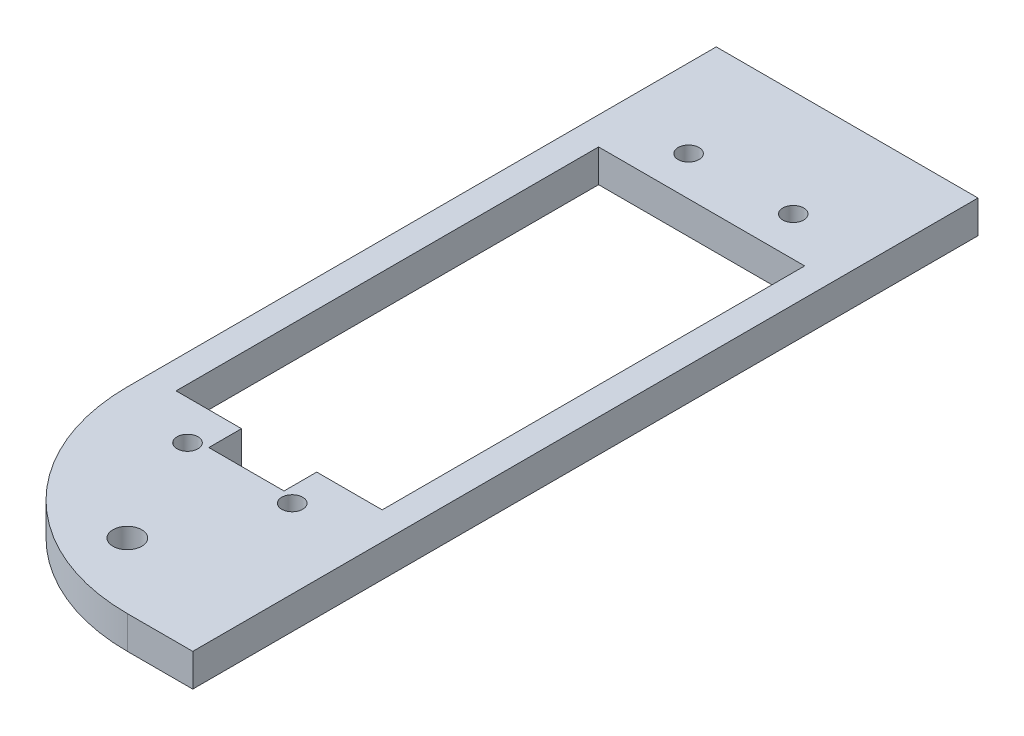
SolidWorks part; units mm, degrees
ref_plane "Front Plane" through (0, 0, 0) normal (0, 0, 1) x (1, 0, 0)
ref_plane "Top Plane" through (0, 0, 0) normal (0, 1, 0) x (1, 0, 0)
ref_plane "Right Plane" through (0, 0, 0) normal (1, 0, 0) x (0, 0, -1)
ref_plane "Plane1" through (0, -3.175, 0) normal (0, -1, 0) x (1, 0, 0)
sketch "Sketch1" plane through (0, -3.175, 0) normal (0, -1, 0) x (1, 0, 0)
  line L0 (12.7, 38.1) -> (6.35, 38.1)
  line L1 (-12.7, 19.05) -> (-12.7, -38.1)
  line L2 (-12.7, -38.1) -> (12.7, -38.1)
  line L3 (12.7, -38.1) -> (12.7, 38.1)
  line L4 (3.65, 17.018) -> (10, 17.018)
  line L5 (10, 17.018) -> (10, -23.982)
  line L6 (10, -23.982) -> (-10, -23.982)
  line L7 (-10, -23.982) -> (-10, 17.018)
  line L8 (-10, 17.018) -> (-3.65, 17.018)
  line L9 (-3.65, 17.018) -> (-3.65, 20.193)
  line L10 (-3.65, 20.193) -> (3.65, 20.193)
  line L11 (3.65, 20.193) -> (3.65, 17.018)
  circle A0 centre (5.08, 20.828) radius 1.016
  circle A1 centre (-5.08, 20.828) radius 1.016
  circle A2 centre (-5.08, -27.792) radius 1.016
  circle A3 centre (5.08, -27.792) radius 1.016
  arc A4 (6.35, 38.1) -> (-12.7, 19.05) centre (6.35, 19.05) ccw
  circle A5 centre (0, 31.75) radius 1.397
extrude "Boss-Extrude1" add sketch "Sketch1" against normal blind 3.175
